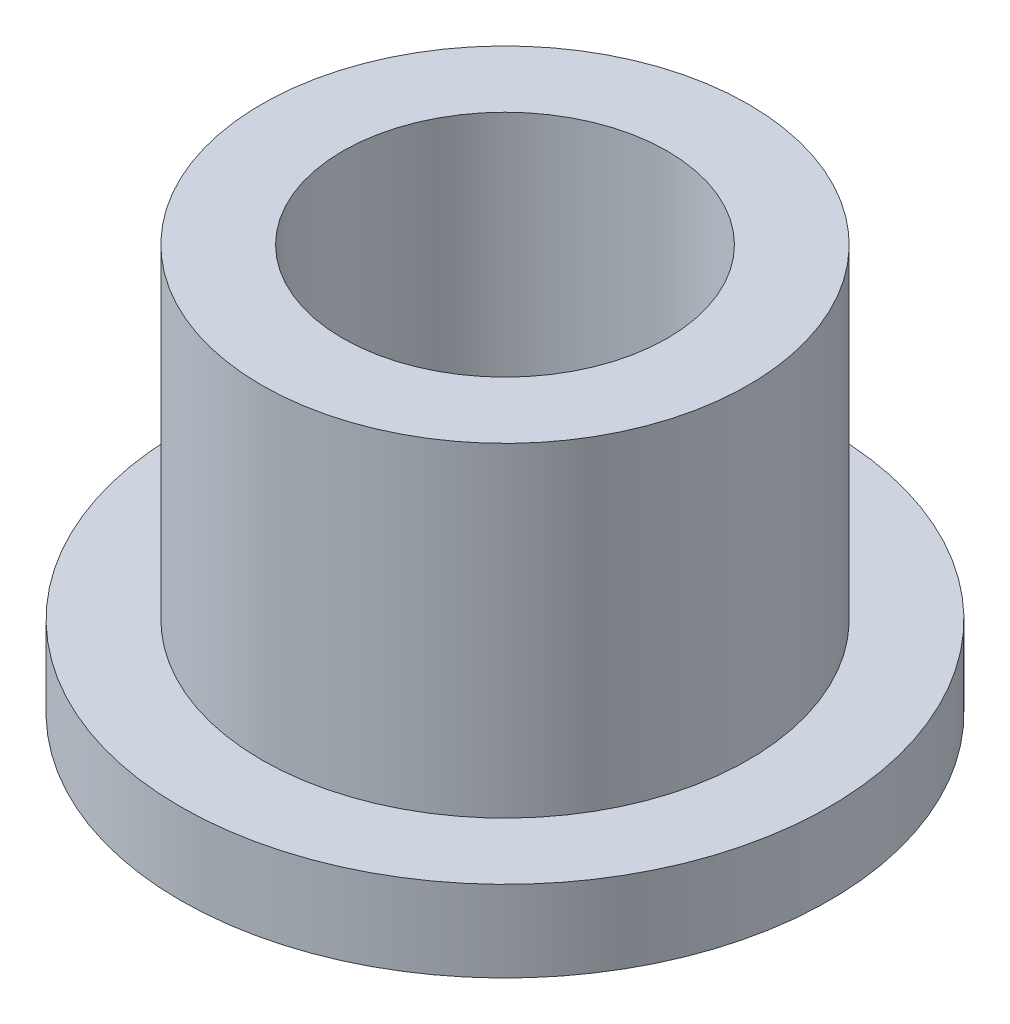
SolidWorks part; units mm, degrees
ref_plane "Front" through (0, 0, 0) normal (0, 0, 1) x (1, 0, 0)
ref_plane "Top" through (0, 0, 0) normal (0, 1, 0) x (1, 0, 0)
ref_plane "Right" through (0, 0, 0) normal (1, 0, 0) x (0, 0, -1)
sketch "Sketch1" plane through (0, 0, 0) normal (0, 1, 0) x (1, 0, 0)
  circle A0 centre (0, 0) radius 3.175
  circle A1 centre (0, 0) radius 4.7625
  circle A2 centre (0, 0) radius 6.35
  dimension "ID" = 6.35
  dimension "OD" = 9.525
  dimension "FlangeOD" = 12.7
sketch "Sketch2" plane through (0, 0, 0) normal (0, 1, 0) x (1, 0, 0)
  circle A0 centre (0, 0) radius 3.175 construction
  circle A1 centre (0, 0) radius 4.7625 construction
  circle A2 centre (0, 0) radius 3.175
  circle A3 centre (0, 0) radius 4.7625
extrude "Boss-Extrude1" add sketch "Sketch2" along normal blind 7.9375
sketch "Sketch3" plane through (0, 0, 0) normal (0, 1, 0) x (1, 0, 0)
  circle A0 centre (0, 0) radius 6.35 construction
  circle A1 centre (0, 0) radius 4.7625 construction
  circle A2 centre (0, 0) radius 6.35
  circle A3 centre (0, 0) radius 4.7625
extrude "Boss-Extrude2" add sketch "Sketch3" along normal blind 1.5875
